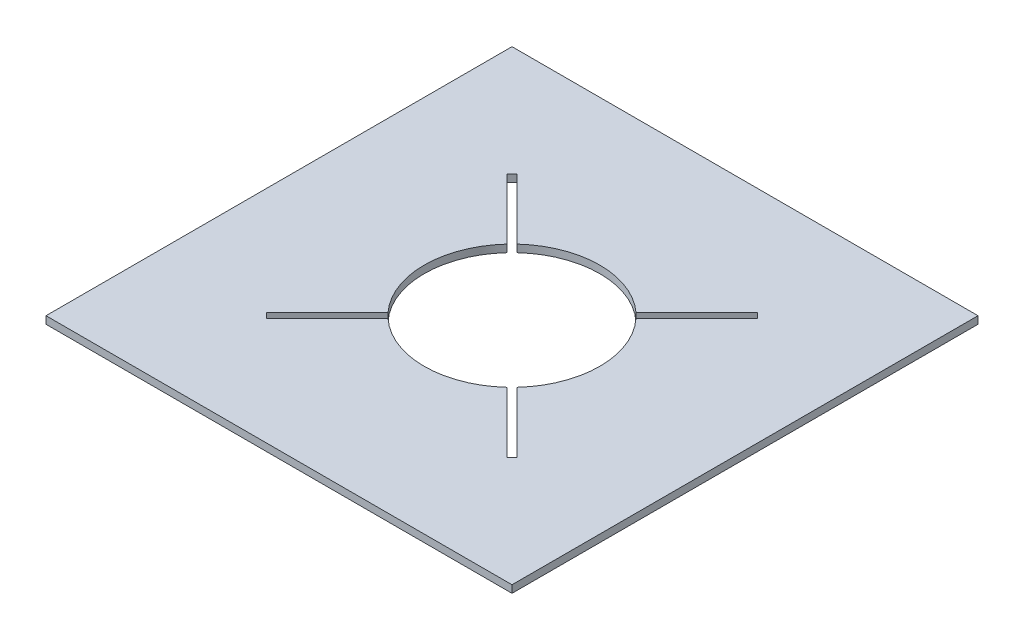
SolidWorks part; units mm, degrees
ref_plane "Front Plane" through (0, 0, 0) normal (0, 0, 1) x (1, 0, 0)
ref_plane "Top Plane" through (0, 0, 0) normal (0, 1, 0) x (1, 0, 0)
ref_plane "Right Plane" through (0, 0, 0) normal (1, 0, 0) x (0, 0, -1)
sketch "Sketch4" plane through (0, 0, 0) normal (0, 1, 0) x (1, 0, 0)
  line L1 (-206.5459, -206.5459) -> (206.5459, -206.5459)
  line L2 (-206.5459, -206.5459) -> (-206.5459, 206.5459)
  line L3 (-206.5459, 206.5459) -> (206.5459, 206.5459)
  line L4 (206.5459, -206.5459) -> (206.5459, 206.5459)
  line L5 (-206.5459, -206.5459) -> (206.5459, 206.5459) construction
  line L6 (-206.5459, 206.5459) -> (206.5459, -206.5459) construction
  circle A0 centre (0, 0) radius 77.7926
  point P0 (0, 0)
extrude "Boss-Extrude3" add sketch "Sketch4" along normal blind 6.604 contours L3 L4 L1 L2
sketch "Sketch6" plane through (0, 6.604, 0) normal (0, 1, 0) x (1, 0, 0)
  circle A0 centre (0, 0) radius 77.7926
extrude "Cut-Extrude1" cut sketch "Sketch6" against normal blind 6.604
sketch "Sketch8" plane through (0, 6.604, 0) normal (0, 1, 0) x (1, 0, 0)
  line L4 (-111.1935, -106.5956) -> (106.5956, 111.1935)
  line L5 (-111.1935, -106.5956) -> (-106.5956, -111.1935)
  line L6 (106.5956, 111.1935) -> (111.1935, 106.5956)
  line L7 (-106.5956, -111.1935) -> (111.1935, 106.5956)
  line L8 (-111.1935, -106.5956) -> (111.1935, 106.5956) construction
  line L9 (106.5956, 111.1935) -> (-106.5956, -111.1935) construction
  point P3 (0, 0)
extrude "Cut-Extrude2" cut sketch "Sketch8" against normal blind 6.604
sketch "Sketch9" plane through (0, 6.604, 0) normal (0, 1, 0) x (1, 0, 0)
  line L0 (111.2025, -106.5867) -> (-106.5867, 111.2025)
  line L1 (111.2025, -106.5867) -> (106.5867, -111.2025)
  line L2 (-106.5867, 111.2025) -> (-111.2025, 106.5867)
  line L3 (106.5867, -111.2025) -> (-111.2025, 106.5867)
  line L4 (111.2025, -106.5867) -> (-111.2025, 106.5867) construction
  line L5 (-106.5867, 111.2025) -> (106.5867, -111.2025) construction
  point P1 (0, 0)
extrude "Cut-Extrude3" cut sketch "Sketch9" against normal blind 6.604
